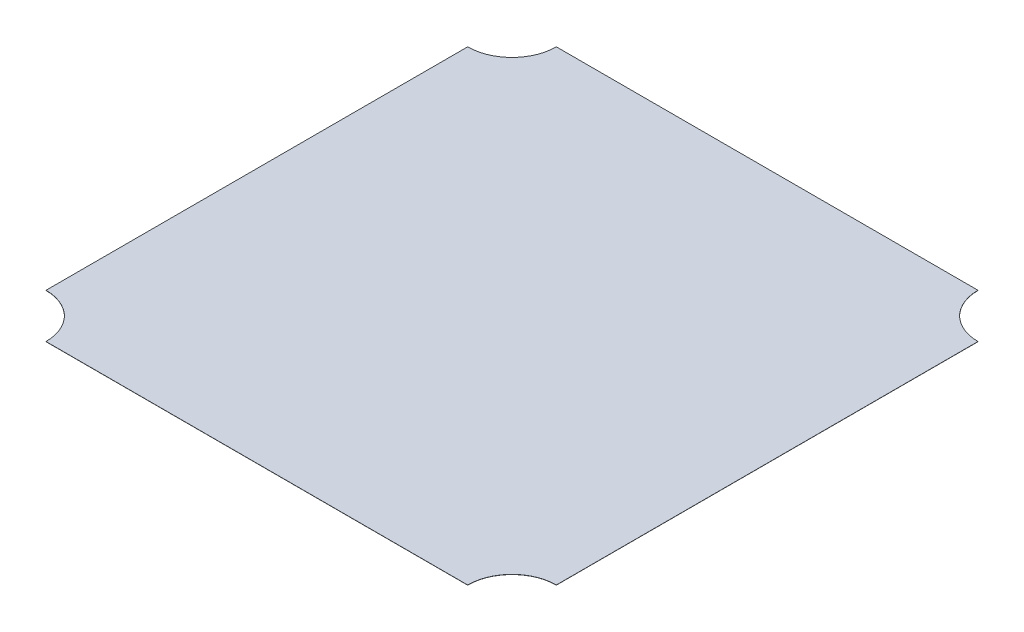
SolidWorks part; units mm, degrees
ref_plane "Front Plane" through (0, 0, 0) normal (0, 0, 1) x (1, 0, 0)
ref_plane "Top Plane" through (0, 0, 0) normal (0, 1, 0) x (1, 0, 0)
ref_plane "Right Plane" through (0, 0, 0) normal (1, 0, 0) x (0, 0, -1)
sketch "Sketch1" plane through (0, 0, 0) normal (0, 0, 1) x (1, 0, 0)
  line L0 (0, 0.0254) -> (0, -0.0254)
  line L1 (-76.2, 0) -> (76.2, 0) construction
  point P6 (0, 0)
  dimension "Width" = 152.4
  dimension "Wire Dia" = 0.0508
sketch "Sketch2" plane through (0, 0, 0) normal (1, 0, 0) x (0, 0, -1)
  line L0 (76.2, 0) -> (-76.2, 0)
  line L2 (76.2, -0.0254) -> (-76.2, -0.0254) construction
  line L3 (76.2, -0.0254) -> (76.2, 0.0254) construction
  line L4 (76.2, 0.0254) -> (-76.2, 0.0254) construction
  line L5 (-76.2, -0.0254) -> (-76.2, 0.0254) construction
  line L6 (76.2, -0.0254) -> (-76.2, 0.0254) construction
  line L7 (76.2, 0.0254) -> (-76.2, -0.0254) construction
  point P0 (0, 0)
  point P4 (0, 0)
  point P10 (-76.2, 0.0254)
  point P12 (-76.2, -0.0254)
  point P13 (76.2, 0.0254)
  point P14 (76.2, -0.0254)
  dimension "Length" = 152.4
sketch "Sketch3" plane through (0, 0, 0) normal (0, 0, 1) x (1, 0, 0)
  line L1 (76.2, 0.0254) -> (-76.2, 0.0254)
  line L2 (76.2, 0.0254) -> (76.2, -0.0254)
  line L3 (76.2, -0.0254) -> (-76.2, -0.0254)
  line L4 (-76.2, 0.0254) -> (-76.2, -0.0254)
  line L5 (76.2, 0.0254) -> (-76.2, -0.0254) construction
  line L6 (76.2, -0.0254) -> (-76.2, 0.0254) construction
  point P0 (0, 0)
extrude "Boss-Extrude1" add sketch "Sketch3" along normal up to vertex (76.2 mm away) and the other way up to vertex (76.2 mm away) up to point (0, 0, 76.2) other way up to point (0, 0, -76.2)
sketch "Sketch4" plane through (0, 0, 0) normal (0, 1, 0) x (1, 0, 0)
  line L1 (76.2, -76.2) -> (-76.2, -76.2) construction
  line L2 (76.2, -76.2) -> (76.2, 76.2) construction
  line L3 (76.2, 76.2) -> (-76.2, 76.2) construction
  line L4 (-76.2, -76.2) -> (-76.2, 76.2) construction
  line L5 (76.2, -76.2) -> (-76.2, 76.2) construction
  line L6 (76.2, 76.2) -> (-76.2, -76.2) construction
  point P0 (0, 0)
  point P6 (-76.2, 76.2)
  point P10 (76.2, 76.2)
  point P11 (76.2, -76.2)
  point P12 (-76.2, -76.2)
sketch "Sketch7" plane through (0, 0.0254, 0) normal (0, 1, 0) x (1, 0, 0)
  line L0 (-129.3655, 135.5611) -> (124.6345, 135.5611)
  line L1 (-129.3655, 135.5611) -> (-129.3655, -118.4389)
  line L2 (-129.3655, -118.4389) -> (124.6345, -118.4389)
  line L3 (124.6345, 135.5611) -> (124.6345, -118.4389)
  line L4 (-76.2, 76.2) -> (-76.2, -69.85)
  line L5 (-76.2, 76.2) -> (69.85, 76.2)
  line L6 (-76.2, -69.85) -> (69.85, -69.85)
  line L7 (69.85, 76.2) -> (69.85, -69.85)
  circle A0 centre (69.85, -69.85) radius 12.7
  circle A1 centre (69.85, 76.2) radius 12.7
  circle A2 centre (-76.2, 76.2) radius 12.7
  circle A3 centre (-76.2, -69.85) radius 12.7
  point P13 (0, 0)
  line M11 (76.2, -76.2) -> (76.2, 76.2)
  line M12 (76.2, 76.2) -> (-76.2, 76.2)
  line M13 (-76.2, 76.2) -> (-76.2, -76.2)
  line M14 (-76.2, -76.2) -> (76.2, -76.2)
extrude "Cut-Extrude4" cut sketch "Sketch7" against normal mid plane 50.8 contours L6 A3 M13 | A2 M13 M12 | A1 L7 M12 | L7 A0 L6 | A3 A0 L6 M14 | A1 L7 A0 M11 | A0 L7 L6 M11 M14 | L7 A1 M11 M12 | A3 L6 M14 M13 | L0 L3 L2 L1
